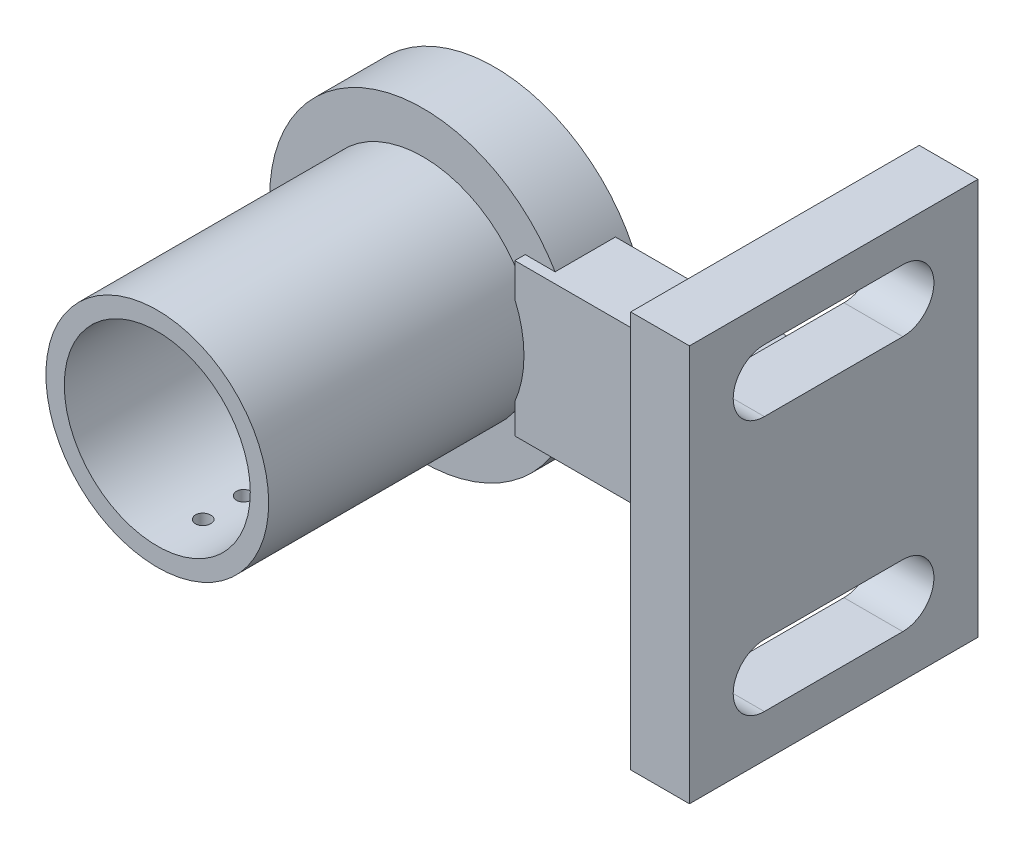
SolidWorks part; units mm, degrees
ref_plane "Front Plane" through (0, 0, 0) normal (0, 0, 1) x (1, 0, 0)
ref_plane "Top Plane" through (0, 0, 0) normal (0, 1, 0) x (1, 0, 0)
ref_plane "Right Plane" through (0, 0, 0) normal (1, 0, 0) x (0, 0, -1)
sketch "Sketch1" plane through (0, 0, 0) normal (0, 0, 1) x (1, 0, 0)
  circle A0 centre (0, 0) radius 15
  circle A1 centre (0, 0) radius 9.1
sketch "Sketch2" plane through (0, 0, 3) normal (0, 0, 1) x (1, 0, 0)
  circle A0 centre (0, 0) radius 13.05
  circle A1 centre (0, 0) radius 15
extrude "Boss-Extrude2" add sketch "Sketch2" against normal blind 8 and the other way blind 16
extrude "Boss-Extrude3" add sketch "Sketch1" along normal blind 28
ref_plane "Plane1" through (0, 0, 0) normal (0, 0, -1) x (-1, 0, 0)
sketch "Sketch4" plane through (0, 0, 0) normal (0, 0, -1) x (-1, 0, 0)
  circle A0 centre (0, 0) radius 15
  circle A1 centre (0, 0) radius 10.9
extrude "Cut-Extrude2" cut sketch "Sketch4" against normal blind 29
ref_plane "Plane2" through (10, 0, 0) normal (1, 0, 0) x (0, 0, -1)
sketch "Sketch5" plane through (10, 0, 0) normal (1, 0, 0) x (0, 0, -1)
  line L0 (-3.0202, 7.6053) -> (-3.0202, -7.2518)
  line L1 (3.901, 7.6053) -> (-3.0202, 7.6053)
  line L2 (3.901, -7.2518) -> (-3.0202, -7.2518)
  line L3 (3.901, 7.6053) -> (3.901, -7.2518)
extrude "Boss-Extrude4" add sketch "Sketch5" along normal blind 22
ref_plane "Plane3" through (0, 0, 0) normal (0, 0, 1) x (1, 0, 0)
sketch "Sketch3" plane through (0, 0, 0) normal (0, 1, 0) x (1, 0, 0)
  line L0 (0, 0) -> (0, -28.107) construction
  circle A0 centre (0, -3.5) radius 0.75
  circle A1 centre (0, -7.5) radius 0.75
  circle A2 centre (0, -11.5) radius 0.75
  circle A3 centre (0, -15.5) radius 0.75
  circle A4 centre (0, -19.5) radius 0.75
  circle A5 centre (0, -23.5) radius 0.75
  point P3 (0, -3.5)
  point P4 (0, -11.5)
  point P5 (0, -7.5)
  point P6 (0, -15.5)
  point P7 (0, -19.5)
  point P8 (0, -23.5)
  dimension "D1" = 3.5
  dimension "D2" = 4
  dimension "D3" = 4
  dimension "D4" = 4
  dimension "D5" = 4
  dimension "D6" = 4
extrude "Cut-Extrude1" cut sketch "Sketch3" against normal through all
sketch "Sketch6" plane through (0, 0, 0) normal (0, 0, 1) x (1, 0, 0)
  circle A0 centre (0, 0) radius 10.9
  circle A1 centre (0, 0) radius 15
extrude "Boss-Extrude5" add sketch "Sketch6" along normal blind 2
sketch "Sketch7" plane through (32, 0, 0) normal (1, 0, 0) x (0, 0, -1)
  line L0 (3.901, 7.6053) -> (-3.0202, -7.2518) construction
  line L1 (-3.0202, 7.6053) -> (3.901, -7.2518) construction
  line L3 (14.5568, 19.5822) -> (-13.6761, 19.5822)
  line L4 (14.5568, 19.5822) -> (14.5568, -19.2287)
  line L5 (14.5568, -19.2287) -> (-13.6761, -19.2287)
  line L6 (-13.6761, 19.5822) -> (-13.6761, -19.2287)
  line L7 (14.5568, 19.5822) -> (-13.6761, -19.2287) construction
  line L8 (14.5568, -19.2287) -> (-13.6761, 19.5822) construction
  point P8 (0.4404, 0.1767)
extrude "Boss-Extrude6" add sketch "Sketch7" along normal blind 5.75
sketch "Sketch9" plane through (32, 0, 0) normal (-1, 0, 0) x (0, 0, 1)
  line L0 (-7.1928, 16.0247) -> (6.3478, 16.0247)
  line L1 (-7.1928, 9.9247) -> (6.3478, 9.9247)
  line L2 (-7.1928, -8.9672) -> (6.3478, -8.9672)
  line L3 (-7.1928, -15.0672) -> (6.3478, -15.0672)
  arc A0 (-7.1928, 16.0247) -> (-7.1928, 9.9247) centre (-7.1928, 12.9747) ccw
  arc A1 (6.3478, 9.9247) -> (6.3478, 16.0247) centre (6.3478, 12.9747) ccw
  arc A2 (6.3478, -15.0672) -> (6.3478, -8.9672) centre (6.3478, -12.0172) ccw
  arc A3 (-7.1928, -8.9672) -> (-7.1928, -15.0672) centre (-7.1928, -12.0172) ccw
extrude "Cut-Extrude3" cut sketch "Sketch9" against normal blind 8
sketch "Sketch10" plane through (0, -7.2518, 0) normal (0, -1, 0) x (1, 0, 0)
  line L0 (32, 3.0202) -> (10, 3.0202) construction
  line L1 (13.1306, -3.901) -> (23.1306, -3.901)
  line L2 (13.1306, -3.901) -> (13.1306, 3.0202)
  line L3 (13.1306, 3.0202) -> (23.1306, 3.0202)
  line L4 (23.1306, -3.901) -> (23.1306, 3.0202)
extrude "Boss-Extrude7" [suppressed] add sketch "Sketch10" along normal blind 30
sketch "Sketch11" [suppressed] plane through (13.1306, 0, 0) normal (-1, 0, 0) x (0, 0, 1)
  line L0 (-3.901, -37.2518) -> (-3.901, -7.2518) construction
  line L1 (3.0202, -37.2518) -> (-3.901, -37.2518)
  line L2 (3.0202, -37.2518) -> (3.0202, -27.2518)
  line L3 (3.0202, -27.2518) -> (-3.901, -27.2518)
  line L4 (-3.901, -37.2518) -> (-3.901, -27.2518)
extrude "Boss-Extrude8" [suppressed] add sketch "Sketch11" along normal blind 36.5
sketch "Sketch13" [suppressed] plane through (0, 0, -3.901) normal (0, 0, -1) x (-1, 0, 0)
  line L0 (23.1033, -27.2518) -> (23.1033, 0)
  line L1 (23.1033, -27.2518) -> (13.1033, -27.2518) construction
  line L2 (0, 0) -> (0, -43.7758) construction
  line L3 (23.1033, -27.2518) -> (13.1866, -27.2518)
  line L4 (23.3694, -27.2518) -> (-13.1306, -27.2518) construction
  line L5 (23.1033, -27.2518) -> (13.1866, -27.2518)
  line L6 (13.1866, -27.2518) -> (13.1866, -4.9753)
  line L7 (0, 0) -> (-16.5193, -30.7521) construction
  line L8 (16.5193, -30.7521) -> (-16.5193, -30.7521)
  line L9 (-16.5193, -30.7521) -> (-23.1306, -30.7521) construction
  line L10 (-23.1306, -37.2518) -> (-23.1306, -7.2518) construction
  line L11 (16.5193, -30.7521) -> (23.1293, -30.7521) construction
  line L12 (13.1866, -27.2518) -> (23.1033, -27.2518)
  line L13 (23.1033, 0) -> (14.094, 0)
  arc A0 (-16.7228, 0.1971) -> (-16.7237, 0.0924) centre (0, 0) ccw
  arc A2 (13.1866, -4.9753) -> (14.094, 0) centre (0, 0) ccw
  point P17 (0, -30.7521)
  dimension "D1" = 28.244
extrude "Boss-Extrude9" [suppressed] add sketch "Sketch13" against normal blind 7
sketch "Sketch14" [suppressed] plane through (0, 0, -3.901) normal (0, 0, -1) x (-1, 0, 0)
  line L0 (-13.1306, -27.2518) -> (-23.1306, -27.2518) construction
  line L1 (-23.1306, -37.2518) -> (-23.1306, -7.2518) construction
  line L2 (-23.1306, -27.2518) -> (-23.1306, -37.2518) construction
  line L3 (-23.1306, -32.2518) -> (23.3694, -32.2518) construction
  line L4 (23.3694, -27.2518) -> (23.3694, -37.2518) construction
  line L5 (-13.1306, -27.2518) -> (-23.1306, -37.2518) construction
  line L6 (13.1866, -27.2518) -> (23.3694, -37.2518) construction
  circle A0 centre (18.278, -32.2518) radius 4
  circle A1 centre (-18.145, -32.2518) radius 4
extrude "Cut-Extrude5" [suppressed] cut sketch "Sketch14" against normal through all
sketch "Sketch15" plane through (0, 0, -5) normal (0, 0, -1) x (-1, 0, 0)
  circle A0 centre (0, 0) radius 13
extrude "Cut-Extrude6" cut sketch "Sketch15" against normal blind 5
